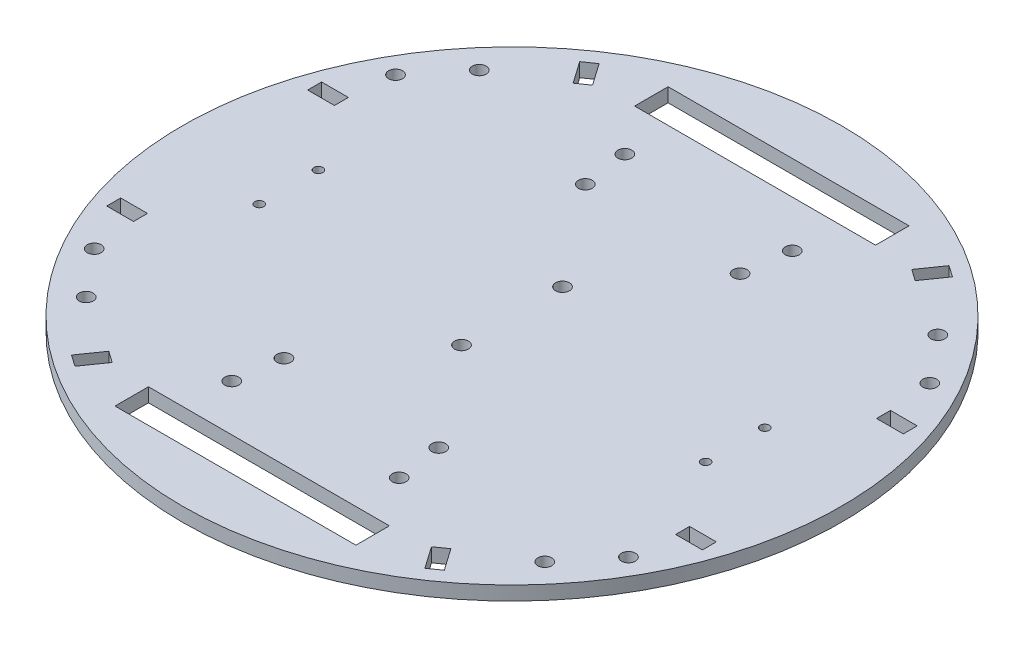
SolidWorks part; units mm, degrees
ref_plane "Front" through (0, 0, 0) normal (0, 0, 1) x (1, 0, 0)
ref_plane "Top" through (0, 0, 0) normal (0, 1, 0) x (1, 0, 0)
ref_plane "Right" through (0, 0, 0) normal (1, 0, 0) x (0, 0, -1)
sketch "Sketch1" plane through (0, 0, 0) normal (0, 1, 0) x (1, 0, 0)
  circle A0 centre (0, 0) radius 75
  dimension "D1" = 150
extrude "Boss-Extrude1" add sketch "Sketch1" along normal blind 3.175
sketch "Sketch2" plane through (0, 3.175, 0) normal (0, 1, 0) x (1, 0, 0)
  line L0 (0, 0) -> (0, 59.1292) construction
  line L1 (-27.4131, 62.9392) -> (27.4131, 62.9392)
  line L2 (-27.4131, 62.9392) -> (-27.4131, 55.3192)
  line L3 (-27.4131, 55.3192) -> (27.4131, 55.3192)
  line L4 (27.4131, 62.9392) -> (27.4131, 55.3192)
  line L5 (-27.4131, 62.9392) -> (27.4131, 55.3192) construction
  line L6 (-27.4131, 55.3192) -> (27.4131, 62.9392) construction
  line L7 (-27.4131, -55.3192) -> (27.4131, -55.3192)
  line L8 (-27.4131, -55.3192) -> (-27.4131, -62.9392)
  line L9 (-27.4131, -62.9392) -> (27.4131, -62.9392)
  line L10 (27.4131, -55.3192) -> (27.4131, -62.9392)
  line L11 (-27.4131, -55.3192) -> (27.4131, -62.9392) construction
  line L12 (-27.4131, -62.9392) -> (27.4131, -55.3192) construction
  line L13 (0, 0) -> (0, -59.1292) construction
  line L14 (-27.4131, 62.9392) -> (-29.9487, 68.761) construction
  line L15 (27.4131, 62.9392) -> (29.9487, 68.761) construction
  line L16 (-29.9487, 68.761) -> (29.9487, 68.761) construction
  line L17 (-36.3936, 65.9539) -> (-23.5039, 71.568) construction
  circle A0 centre (0, 0) radius 75 construction
  point P0 (0, 59.1292)
  point P5 (0, -59.1292)
  dimension "D1" = 6.35
  dimension "D2" = 7.62
  dimension "D3" = 54.8262
extrude "Cut-Extrude1" cut sketch "Sketch2" against normal up to surface (3.175 mm away) up to face at (0, 0, 75)
ref_plane "Plane1" through (0, 0, 59.1292) normal (0, 0, 1) x (1, 0, 0)
sketch "Sketch4" plane through (0, 3.175, 0) normal (0, 1, 0) x (1, 0, 0)
  circle A0 centre (-52.1803, 44.7298) radius 1.5875
  circle A1 centre (-19.05, 44.7298) radius 1.5875
  circle A2 centre (-60.7918, 34.29) radius 1.5875
  circle A3 centre (-17.6118, 34.29) radius 1.5875
  circle A4 centre (-60.7918, -34.29) radius 1.5875
  circle A5 centre (-52.1803, -44.7298) radius 1.5875
  circle A6 centre (-17.6118, -34.29) radius 1.5875
  circle A7 centre (-19.05, -44.7298) radius 1.5875
  circle A8 centre (17.6118, -34.29) radius 1.5875
  circle A9 centre (19.05, -44.7298) radius 1.5875
  circle A10 centre (52.1803, -44.7298) radius 1.5875
  circle A11 centre (60.7918, -34.29) radius 1.5875
  circle A12 centre (60.7918, 34.29) radius 1.5875
  circle A13 centre (52.1803, 44.7298) radius 1.5875
  circle A14 centre (19.05, 44.7298) radius 1.5875
  circle A15 centre (17.6118, 34.29) radius 1.5875
  circle A16 centre (0, 11.4942) radius 1.5875
  circle A17 centre (0, -11.4942) radius 1.5875
  dimension "D1" = 3.175
extrude "Cut-Extrude2" cut sketch "Sketch4" against normal up to surface (3.175 mm away) up to face at (0, 0, 59.1292)
sketch "Sketch5" plane through (0, 3.175, 0) normal (0, 1, 0) x (1, 0, 0)
  line L0 (-39.37, -56.239) -> (0, 0) construction
  line L1 (61.6841, 24.4475) -> (67.7801, 24.4475)
  line L2 (61.6841, 24.4475) -> (61.6841, 21.2725)
  line L3 (61.6841, 21.2725) -> (67.7801, 21.2725)
  line L4 (67.7801, 24.4475) -> (67.7801, 21.2725)
  line L5 (61.6841, 24.4475) -> (67.7801, 21.2725) construction
  line L6 (61.6841, 21.2725) -> (67.7801, 24.4475) construction
  line L7 (61.6841, -21.2725) -> (67.7801, -21.2725)
  line L8 (61.6841, -21.2725) -> (61.6841, -24.4475)
  line L9 (61.6841, -24.4475) -> (67.7801, -24.4475)
  line L10 (67.7801, -21.2725) -> (67.7801, -24.4475)
  line L11 (61.6841, -21.2725) -> (67.7801, -24.4475) construction
  line L12 (61.6841, -24.4475) -> (67.7801, -21.2725) construction
  line L13 (-67.7801, -21.2725) -> (-61.6841, -21.2725)
  line L14 (-67.7801, -21.2725) -> (-67.7801, -24.4475)
  line L15 (-67.7801, -24.4475) -> (-61.6841, -24.4475)
  line L16 (-61.6841, -21.2725) -> (-61.6841, -24.4475)
  line L17 (-67.7801, -21.2725) -> (-61.6841, -24.4475) construction
  line L18 (-67.7801, -24.4475) -> (-61.6841, -21.2725) construction
  line L19 (-67.7801, 24.4475) -> (-61.6841, 24.4475)
  line L20 (-67.7801, 24.4475) -> (-67.7801, 21.2725)
  line L21 (-67.7801, 21.2725) -> (-61.6841, 21.2725)
  line L22 (-61.6841, 24.4475) -> (-61.6841, 21.2725)
  line L23 (-67.7801, 24.4475) -> (-61.6841, 21.2725) construction
  line L24 (-67.7801, 21.2725) -> (-61.6841, 24.4475) construction
  line L25 (39.8175, 59.6464) -> (42.4185, 57.8256)
  line L26 (39.8175, 59.6464) -> (36.3215, 54.6525)
  line L27 (36.3215, 54.6525) -> (38.9225, 52.8316)
  line L28 (42.4185, 57.8256) -> (38.9225, 52.8316)
  line L29 (39.8175, 59.6464) -> (38.9225, 52.8316) construction
  line L30 (36.3215, 54.6525) -> (42.4185, 57.8256) construction
  line L31 (38.9225, -52.8316) -> (42.4185, -57.8256)
  line L32 (38.9225, -52.8316) -> (36.3215, -54.6525)
  line L33 (36.3215, -54.6525) -> (39.8175, -59.6464)
  line L34 (42.4185, -57.8256) -> (39.8175, -59.6464)
  line L35 (38.9225, -52.8316) -> (39.8175, -59.6464) construction
  line L36 (36.3215, -54.6525) -> (42.4185, -57.8256) construction
  line L37 (-38.9225, -52.8316) -> (-36.3215, -54.6525)
  line L38 (-38.9225, -52.8316) -> (-42.4185, -57.8256)
  line L39 (-42.4185, -57.8256) -> (-39.8175, -59.6464)
  line L40 (-36.3215, -54.6525) -> (-39.8175, -59.6464)
  line L41 (-38.9225, -52.8316) -> (-39.8175, -59.6464) construction
  line L42 (-42.4185, -57.8256) -> (-36.3215, -54.6525) construction
  line L43 (-39.8175, 59.6464) -> (-36.3215, 54.6525)
  line L44 (-39.8175, 59.6464) -> (-42.4185, 57.8256)
  line L45 (-42.4185, 57.8256) -> (-38.9225, 52.8316)
  line L46 (-36.3215, 54.6525) -> (-38.9225, 52.8316)
  line L47 (-39.8175, 59.6464) -> (-38.9225, 52.8316) construction
  line L48 (-42.4185, 57.8256) -> (-36.3215, 54.6525) construction
  line L49 (0, 0) -> (39.37, 56.239) construction
  line L50 (-39.37, 56.239) -> (0, 0) construction
  line L51 (0, 0) -> (39.37, -56.239) construction
  line L52 (0, 0) -> (64.7321, 22.86) construction
  line L53 (0, 0) -> (64.7321, -22.86) construction
  line L54 (-64.7321, 22.86) -> (0, 0) construction
  line L55 (0, 0) -> (-64.7321, -22.86) construction
  line L56 (64.7321, 22.86) -> (64.7321, -22.86) construction
  line L57 (-64.7321, 22.86) -> (-64.7321, -22.86) construction
  line L58 (64.7321, 22.86) -> (70.7197, 24.9745) construction
  line L59 (39.37, 56.239) -> (31.75, 56.239) construction
  line L60 (31.75, 55.9542) -> (31.75, 62.3042) construction
  line L61 (-39.37, 56.239) -> (-31.75, 56.239) construction
  line L62 (-31.75, 62.3042) -> (-31.75, 55.9542) construction
  line L63 (-64.7321, -22.86) -> (-64.7321, -30.48) construction
  line L64 (-68.5271, -30.48) -> (-21.4218, -30.48) construction
  line L65 (-64.7321, 22.86) -> (64.7321, 22.86) construction
  circle A0 centre (0, 0) radius 75 construction
  point P0 (64.7321, 22.86)
  point P5 (64.7321, -22.86)
  point P10 (-64.7321, -22.86)
  point P15 (-64.7321, 22.86)
  point P20 (39.37, 56.239)
  point P25 (39.37, -56.239)
  point P30 (-39.37, -56.239)
  point P35 (-39.37, 56.239)
  dimension "D1" = 3.175
  dimension "D2" = 6.096
  dimension "D3" = 6.35
  dimension "D4" = 7.62
  dimension "D5" = 7.62
extrude "Cut-Extrude3" cut sketch "Sketch5" against normal up to surface (3.175 mm away) up to face at (0, 0, 13.0817)
sketch "Sketch6" plane through (0, 3.175, 0) normal (0, 1, 0) x (1, 0, 0)
  line L0 (0, 0) -> (50.8, 0) construction
  line L1 (50.8, 0) -> (50.8, 6.731) construction
  line L2 (50.8, 6.731) -> (50.8, 0) construction
  line L3 (50.8, 0) -> (50.8, -6.731) construction
  circle A0 centre (50.8, 6.731) radius 1.016
  circle A1 centre (50.8, -6.731) radius 1.016
  dimension "D2" = 2.032
  dimension "D1" = 50.8
  dimension "D3" = 6.731
extrude "Cut-Extrude4" cut sketch "Sketch6" against normal up to surface (3.175 mm away) up to face at (-39.37, 0, -56.239)
mirror "Mirror1" about plane through (0, 0, 0) normal (1, 0, 0) of "Cut-Extrude4"
equation "\"d\"= 2.75"
equation "\"D3@Sketch2\"=sqr((\"d\"/2)^2-(\"d\"/2-9.78mm)^2)*2+.25in"
